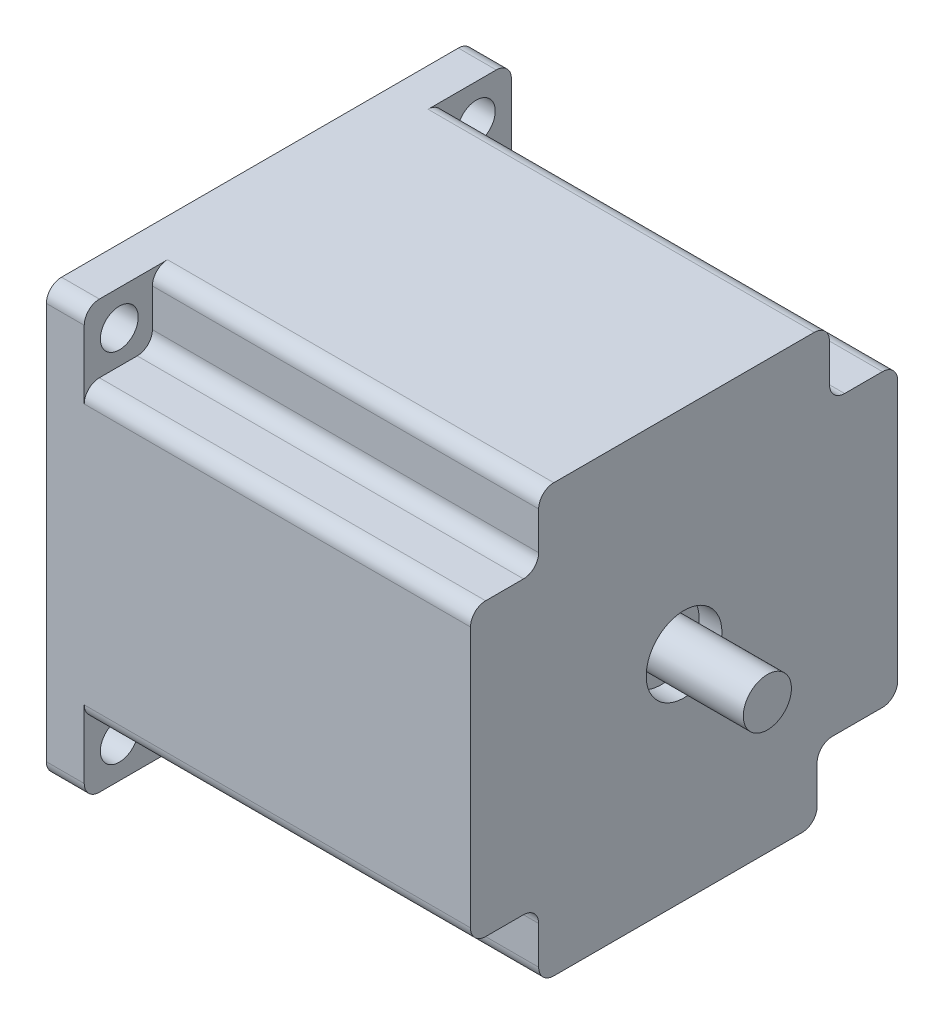
SolidWorks part; units mm, degrees
ref_plane "Front" through (0, 0, 0) normal (0, 0, 1) x (1, 0, 0)
ref_plane "Top" through (0, 0, 0) normal (0, 1, 0) x (1, 0, 0)
ref_plane "Right" through (0, 0, 0) normal (1, 0, 0) x (0, 0, -1)
sketch "Sketch1" plane through (0, 0, 0) normal (1, 0, 0) x (0, 0, -1)
  line L1 (-28.2, 28.2) -> (28.2, 28.2)
  line L2 (-28.2, 28.2) -> (-28.2, -28.2)
  line L3 (-28.2, -28.2) -> (28.2, -28.2)
  line L4 (28.2, 28.2) -> (28.2, -28.2)
  line L5 (-28.2, 28.2) -> (28.2, -28.2) construction
  line L6 (-28.2, -28.2) -> (28.2, 28.2) construction
  line L7 (-23.57, 23.57) -> (23.57, 23.57) construction
  line L8 (-23.57, 23.57) -> (-23.57, -23.57) construction
  line L9 (-23.57, -23.57) -> (23.57, -23.57) construction
  line L10 (23.57, 23.57) -> (23.57, -23.57) construction
  line L11 (-23.57, 23.57) -> (23.57, -23.57) construction
  line L12 (-23.57, -23.57) -> (23.57, 23.57) construction
  circle A0 centre (-23.57, 23.57) radius 2.5
  circle A1 centre (23.57, 23.57) radius 2.5
  circle A2 centre (23.57, -23.57) radius 2.5
  circle A3 centre (-23.57, -23.57) radius 2.5
  point P0 (0, 0)
  point P5 (0, 0)
  dimension "D3" = 5
  dimension "D1" = 56.4
  dimension "D2" = 47.14
extrude "Boss-Extrude1" add sketch "Sketch1" along normal blind 5
sketch "Sketch2" plane through (5, 0, 0) normal (1, 0, 0) x (0, 0, -1)
  line L0 (-19.2, 28.2) -> (-19.2, -28.2) construction
  line L1 (28.2, 28.2) -> (-28.2, 28.2) construction
  line L2 (-28.2, -28.2) -> (28.2, -28.2) construction
  line L3 (19.2, 28.2) -> (19.2, -28.2) construction
  line L4 (-28.2, 19.2) -> (28.2, 19.2) construction
  line L5 (-28.2, 28.2) -> (-28.2, -28.2) construction
  line L6 (28.2, -28.2) -> (28.2, 28.2) construction
  line L7 (-28.2, -19.2) -> (28.2, -19.2) construction
  line L8 (-28.2, 19.2) -> (-19.2, 19.2)
  line L9 (-19.2, 19.2) -> (-19.2, 28.2)
  line L10 (-19.2, 28.2) -> (19.2, 28.2)
  line L11 (19.2, 28.2) -> (19.2, 19.2)
  line L12 (19.2, 19.2) -> (28.2, 19.2)
  line L13 (28.2, 19.2) -> (28.2, -19.2)
  line L14 (28.2, -19.2) -> (17.5666, -19.2)
  line L15 (17.5666, -19.2) -> (17.5666, -28.2)
  line L16 (17.5666, -28.2) -> (-19.2, -28.2)
  line L17 (-19.2, -28.2) -> (-19.2, -19.2)
  line L18 (-19.2, -19.2) -> (-28.2, -19.2)
  line L19 (-28.2, -19.2) -> (-28.2, 19.2)
  dimension "D1" = 9
  dimension "D2" = 9
  dimension "D3" = 9
  dimension "D4" = 9
extrude "Boss-Extrude2" add sketch "Sketch2" along normal blind 51
sketch "Sketch3" plane through (56, 0, 0) normal (1, 0, 0) x (0, 0, -1)
  circle A0 centre (0, 0) radius 5
  dimension "D1" = 10
extrude "Cut-Extrude1" cut sketch "Sketch3" against normal blind 3 contours A0
sketch "Sketch5" plane through (53, 0, 0) normal (1, 0, 0) x (0, 0, -1)
  circle A0 centre (0, 0) radius 3.175
  dimension "D1" = 6.35
extrude "Boss-Extrude3" add sketch "Sketch5" along normal blind 14 contours A0
sketch "Sketch6" plane through (0, 0, 0) normal (-1, 0, 0) x (0, 0, 1)
  circle A0 centre (0, 0) radius 19
  dimension "D1" = 38
extrude "Boss-Extrude4" add sketch "Sketch6" along normal blind 1.5 contours A0
sketch "Sketch7" plane through (-1.5, 0, 0) normal (-1, 0, 0) x (0, 0, 1)
  circle A0 centre (0, 0) radius 5
  dimension "D1" = 10
extrude "Cut-Extrude2" cut sketch "Sketch7" against normal blind 3 contours A0
sketch "Sketch9" plane through (1.5, 0, 0) normal (-1, 0, 0) x (0, 0, 1)
  circle A0 centre (0, 0) radius 3.175
  dimension "D1" = 6.35
extrude "Boss-Extrude5" add sketch "Sketch9" along normal blind 23 contours A0
fillet "Fillet1" radius 2 1 edges at (2.5, 28.2, 28.2)
fillet "Fillet2" radius 2 1 edges at (2.5, 28.2, -28.2)
fillet "Fillet3" radius 2 1 edges at (2.5, -28.2, -28.2)
fillet "Fillet4" radius 2 1 edges at (2.5, -28.2, 28.2)
fillet "Fillet5" radius 2 1 edges at (30.5, 28.2, -19.2)
fillet "Fillet6" radius 2 1 edges at (30.5, 19.2, -28.2)
fillet "Fillet7" radius 2 1 edges at (30.5, -19.2, -28.2)
fillet "Fillet8" radius 2 1 edges at (30.5, -28.2, -17.5666)
fillet "Fillet9" radius 2 1 edges at (30.5, -28.2, 19.2)
fillet "Fillet10" radius 2 1 edges at (30.5, -19.2, 28.2)
fillet "Fillet11" radius 2 1 edges at (30.5, 19.2, 28.2)
fillet "Fillet12" radius 2 1 edges at (30.5, 28.2, 19.2)
fillet "Fillet13" radius 2 1 edges at (30.5, 19.2, -19.2)
fillet "Fillet14" radius 2 1 edges at (30.5, -19.2, -17.5666)
fillet "Fillet15" radius 2 1 edges at (30.5, -19.2, 19.2)
fillet "Fillet16" radius 2 1 edges at (30.5, 19.2, 19.2)
